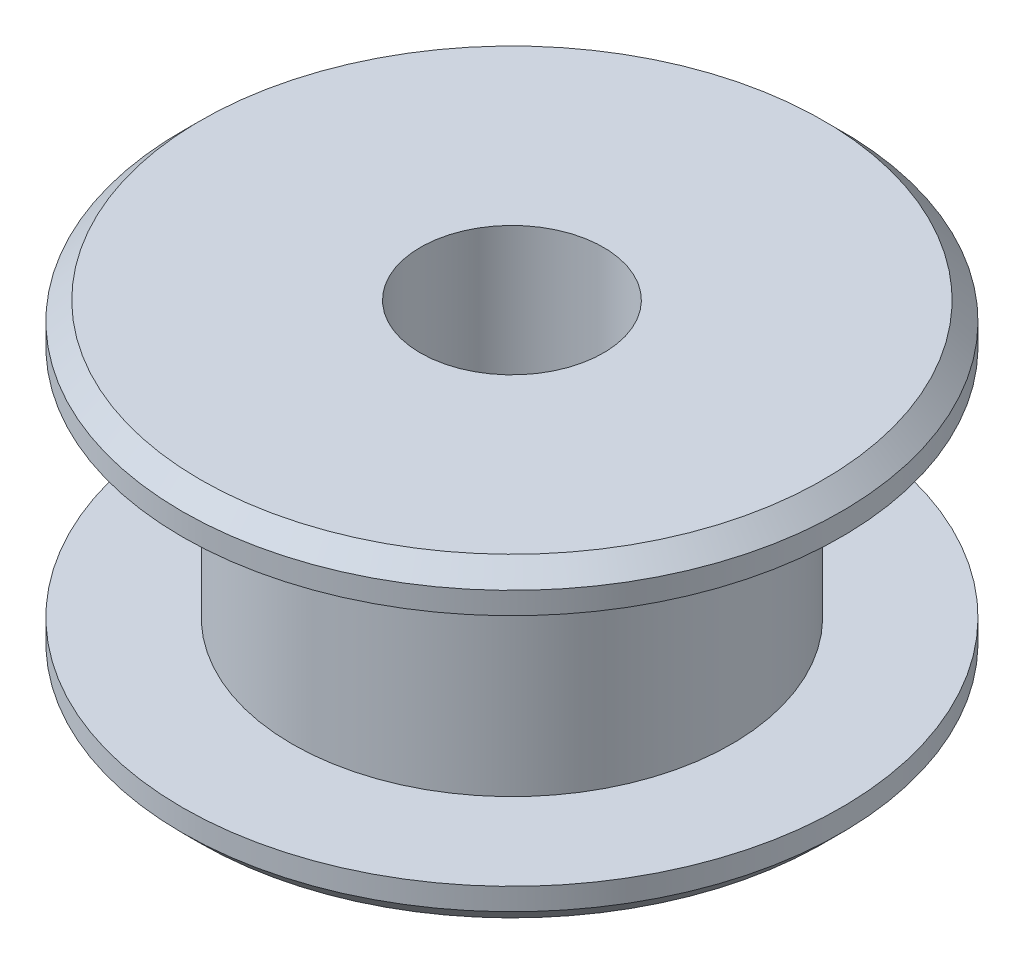
SolidWorks part; units mm, degrees
ref_plane "前视基准面" through (0, 0, 0) normal (0, 0, 1) x (1, 0, 0)
ref_plane "上视基准面" through (0, 0, 0) normal (0, 1, 0) x (1, 0, 0)
ref_plane "右视基准面" through (0, 0, 0) normal (1, 0, 0) x (0, 0, -1)
sketch "草图1" plane through (0, 0, 0) normal (0, 1, 0) x (1, 0, 0)
  circle A0 centre (0, 0) radius 9
  dimension "D1" = 18
extrude "凸台-拉伸1" add sketch "草图1" along normal blind 1.1
sketch "草图2" plane through (0, 1.1, 0) normal (0, 1, 0) x (1, 0, 0)
  circle A0 centre (0, 0) radius 6
  dimension "D1" = 12
extrude "凸台-拉伸2" add sketch "草图2" along normal blind 6.4
sketch "草图3" plane through (0, 7.5, 0) normal (0, 1, 0) x (1, 0, 0)
  circle A0 centre (0, 0) radius 9
  dimension "D1" = 18
extrude "凸台-拉伸3" add sketch "草图3" along normal blind 1.1
chamfer "倒角1" distance 0.5 angle 45 2 edges at (0, 0, 9) (0, 8.6, 9)
sketch "草图4" plane through (0, 8.6, 0) normal (0, 1, 0) x (1, 0, 0)
  circle A0 centre (0, 0) radius 2.5
  dimension "D1" = 5
extrude "切除-拉伸1" cut sketch "草图4" against normal through all contours A0
